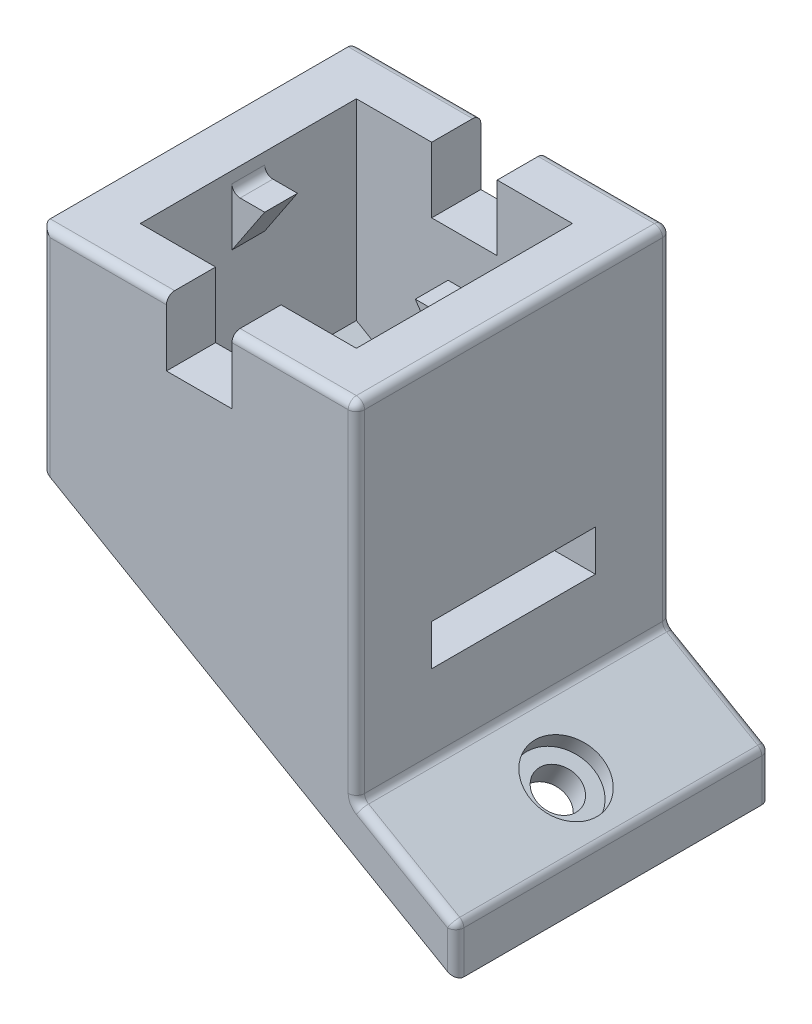
SolidWorks part; units mm, degrees
ref_plane "Front Plane" through (0, 0, 0) normal (0, 0, 1) x (1, 0, 0)
ref_plane "Top Plane" through (0, 0, 0) normal (0, 1, 0) x (1, 0, 0)
ref_plane "Right Plane" through (0, 0, 0) normal (1, 0, 0) x (0, 0, -1)
sketch "Sketch1" plane through (0, 0, 0) normal (0, 1, 0) x (1, 0, 0)
  line L0 (-9.6, 9.6) -> (9.6, 9.6)
  line L1 (-6.6, -6.6) -> (6.6, -6.6)
  line L2 (-6.6, -6.6) -> (-6.6, 6.6)
  line L3 (-6.6, 6.6) -> (6.6, 6.6)
  line L4 (6.6, -6.6) -> (6.6, 6.6)
  line L5 (-6.6, -6.6) -> (6.6, 6.6) construction
  line L6 (-6.6, 6.6) -> (6.6, -6.6) construction
  line L7 (9.6, -9.6) -> (9.6, 9.6)
  line L8 (-9.6, -9.6) -> (9.6, -9.6)
  line L9 (-9.6, -9.6) -> (-9.6, 9.6)
  point P0 (0, 0)
  dimension "D1" = 13.2
  dimension "D2" = 13.2
  dimension "D3" = 3
extrude "Boss-Extrude1" add sketch "Sketch1" against normal blind 30 contours L9 L8 L7 L0 L4 L1 L2 L3
sketch "Sketch2" plane through (0, 0, 9.6) normal (0, 0, 1) x (1, 0, 0)
  line L0 (-9.6, -30) -> (-9.6, -10)
  line L1 (-9.6, -30) -> (-9.6, 0) construction
  line L2 (-9.6, -10) -> (25.041, -30)
  line L3 (25.041, -30) -> (-9.6, -30)
  dimension "D1" = 30
  dimension "D2" = 10
extrude "Cut-Extrude1" cut sketch "Sketch2" against normal blind 30
sketch "Sketch3" plane through (0, 0, 9.6) normal (0, 0, 1) x (1, 0, 0)
  line L0 (-9.6, -10) -> (-9.6, -12.8868)
  line L1 (-9.6, -12.8868) -> (15.6622, -27.4719)
  line L2 (9.6, -21.0851) -> (-9.6, -10) construction
  line L3 (-9.6, -10) -> (15.6622, -24.5851)
  line L4 (15.6622, -24.5851) -> (15.6622, -27.4719)
  dimension "D1" = 2.5
  dimension "D2" = 7
extrude "Boss-Extrude2" add sketch "Sketch3" against normal up to surface (19.2 mm away) up to face at (0, -7.7713, -9.6)
sketch "Sketch4" plane through (-6.7301, -11.6569, 0) normal (0.5, 0.866, 0) x (0.866, -0.5, 0)
  circle A0 centre (22.5587, 0) radius 1.28
  dimension "D1" = 2.56
extrude "Cut-Extrude2" cut sketch "Sketch4" against normal blind 30
sketch "Sketch5" plane through (-6.7301, -11.6569, 0) normal (0.5, 0.866, 0) x (0.866, -0.5, 0)
  circle A0 centre (22.5587, 0) radius 2.18
  dimension "D1" = 4.36
extrude "Cut-Extrude3" cut sketch "Sketch5" against normal blind 1
sketch "Sketch6" plane through (9.6, 0, 0) normal (1, 0, 0) x (0, 0, -1)
  line L0 (0, 0) -> (0, -20.64) construction
  line L1 (-5, -13.75) -> (5, -13.75)
  line L2 (-5, -13.75) -> (-5, -16.25)
  line L3 (-5, -16.25) -> (5, -16.25)
  line L4 (5, -13.75) -> (5, -16.25)
  line L5 (-5, -13.75) -> (5, -16.25) construction
  line L6 (-5, -16.25) -> (5, -13.75) construction
  line L7 (-9.6, 0) -> (9.6, 0) construction
  point P0 (0, -15)
  dimension "D1" = 2.5
  dimension "D2" = 10
  dimension "125" = 15
extrude "Cut-Extrude4" cut sketch "Sketch6" against normal blind 3
ref_plane "Plane1" through (0, 0, 0) normal (0, 0, 1) x (1, 0, 0)
sketch "Sketch7" plane through (0, 0, 0) normal (0, 0, 1) x (1, 0, 0)
  line L0 (-6.6, -1.2) -> (-4.6, -1.2)
  line L1 (-6.6, -11.7321) -> (-6.6, 0) construction
  line L2 (-4.6, -1.2) -> (-6.6, -4.2)
  line L3 (-6.6, -4.2) -> (-6.6, -1.2)
  line L4 (-9.6, 0) -> (9.6, 0) construction
  line L5 (0, 0) -> (0, 6.9288) construction
  line L6 (6.6, -1.2) -> (4.6, -1.2)
  line L7 (4.6, -1.2) -> (6.6, -4.2)
  line L8 (6.6, -4.2) -> (6.6, -1.2)
  dimension "D1" = 3
  dimension "D2" = 2
  dimension "D3" = 1.2
extrude "Boss-Extrude3" add sketch "Sketch7" along normal mid plane 2 contours L3 L2 L0 | L6 L7 L8
sketch "Sketch8" plane through (0, 0, 0) normal (0, 1, 0) x (1, 0, 0)
  line L0 (-9.6, 9.6) -> (9.6, 9.6) construction
  line L1 (-2, 9.6) -> (2, 9.6)
  line L2 (-2, 9.6) -> (-2, 6.6)
  line L3 (-2, 6.6) -> (2, 6.6)
  line L4 (2, 9.6) -> (2, 6.6)
  line L5 (-2, 9.6) -> (2, 6.6) construction
  line L6 (-2, 6.6) -> (2, 9.6) construction
  line L7 (0, 0) -> (-15.535, 0) construction
  line L9 (-13.8942, 0) -> (13.8942, 0) construction
  line L10 (2, -9.6) -> (2, -6.6)
  line L11 (-2, -9.6) -> (2, -9.6)
  line L12 (-2, -9.6) -> (-2, -6.6)
  line L13 (-2, -6.6) -> (2, -6.6)
  point P0 (0, 8.1)
  dimension "D1" = 4
  dimension "D2" = 3
extrude "Cut-Extrude5" cut sketch "Sketch8" against normal blind 4
fillet "Fillet1" radius 0.5 2 edges at (6.6, -1.2, 0) (-6.6, -1.2, 0)
fillet "Fillet2" radius 0.5 15 edges at (12.6311, -22.8351, -9.6) (12.6311, -22.8351, 9.6) (-5.8, 0, -9.6) (-9.6, -6.4434, -9.6) (15.6622, -26.0285, -9.6) (15.6622, -26.0285, 9.6) (15.6622, -24.5851, 0) (9.6, -21.0851, 0) (9.6, -10.5426, -9.6) (5.8, 0, -9.6) (9.6, 0, 0) (5.8, 0, 9.6) (9.6, -10.5426, 9.6) (-9.6, -6.4434, 9.6) (-5.8, 0, 9.6)
